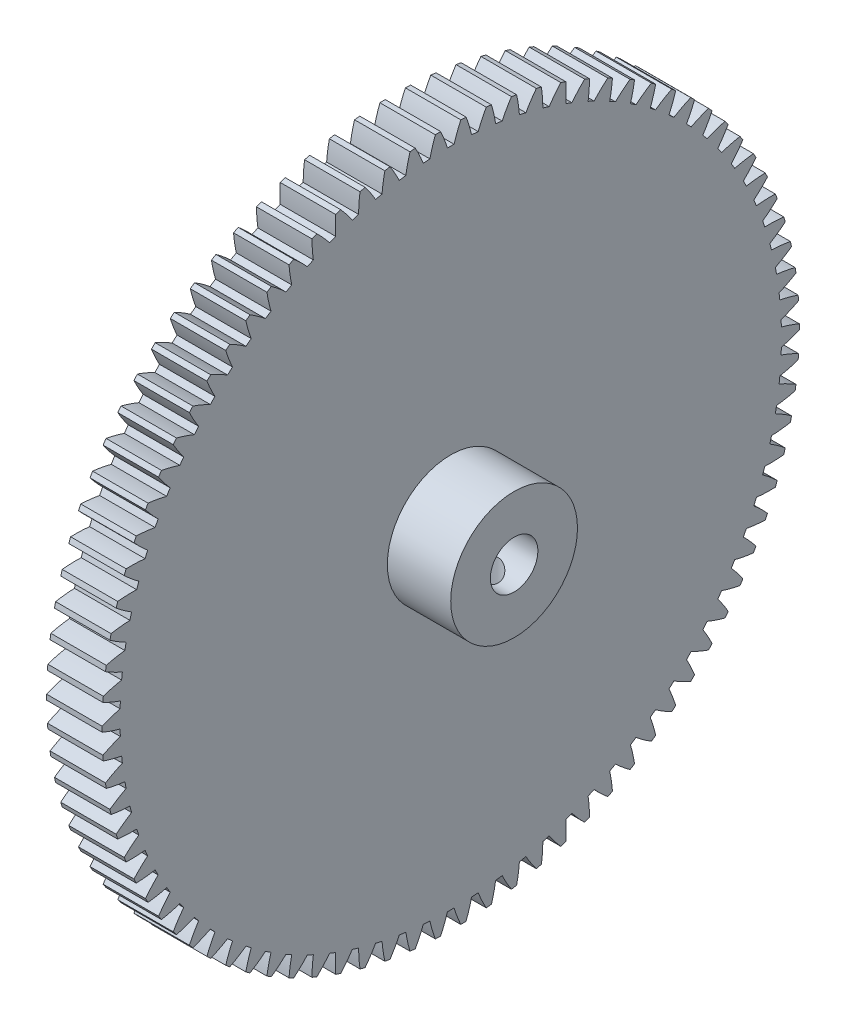
SolidWorks part; units mm, degrees
ref_plane "Plane1" through (0, 0, 0) normal (0, 0, 1) x (1, 0, 0)
ref_plane "Plane2" through (0, 0, 0) normal (0, 1, 0) x (1, 0, 0)
ref_plane "Plane3" through (0, 0, 0) normal (1, 0, 0) x (0, 0, -1)
other "Configuration Table"
sketch "HoldingSke" plane through (0, 0, 0) normal (0, 1, 0) x (1, 0, 0)
  line L0 (0, 0) -> (0.0698, -0.9976)
  line L1 (-15, 0) -> (100, 0) construction
  line L2 (0, 0) -> (-2.1039, 2.3779)
  line L3 (0, 0) -> (-11.863, 4.5341)
  line L4 (0, 0) -> (0.6024, 8.615)
  line L5 (0, 0) -> (-46.8476, -17.4728)
  line L6 (0, 0) -> (-5.8027, -3.9151)
  line L7 (-2.1039, 2.3779) -> (8.6586, 51.2059)
  line L8 (-76.2, 54.61) -> (-75.2, 54.61)
  line L9 (-71.009, 38.7566) -> (-53.1078, 45.2721)
  line L10 (-76.2, 71.12) -> (104.1128, 71.12)
  line L11 (0, 0) -> (-7, 0)
  line L12 (-76.2, 101.6) -> (-76.162, 101.6)
  line L13 (24.9733, 27.94) -> (52.9518, 28.4284)
  line L14 (24.9733, 27.94) -> (24.9743, 27.94)
  line L15 (24.9733, 27.94) -> (100.4006, 29.5858)
  line L16 (-63.627, -1) -> (-12.827, -1)
  circle A0 centre (0, 0) radius 3
  circle A1 centre (0, 0) radius 37.5
  circle A2 centre (0, 0) radius 37.5
  circle A3 centre (0, 0) radius 3
  dimension "MHD" = 75
  dimension "Hub_dia" = 75
  dimension "Bore" = 6
  dimension "MBD" = 6
  dimension "Num_teeth" = 86
  dimension "Pitch" = 1
  dimension "Overall_len" = 50
  dimension "Show_teeth" = 86
  dimension "Thickness" = 7
  dimension "OAL" = 50.0001
  dimension "T_dim" = 1
  dimension "Ap" = 20
  dimension "H" = 19.05
  dimension "Pitch_radius" = 180.3128
  dimension "Width" = 7
  dimension "Backlash" = 0.038
  dimension "Addendum_fac" = 1
  dimension "Dedendum_fac" = 1.25
  dimension "Clearance_fac" = 0.25
  dimension "Dedendum_add" = 0.001
  dimension "Module" = 1
sketch "BasProSke" plane through (0, 0, 0) normal (0, 1, 0) x (1, 0, 0)
  line L0 (-10, 0) -> (60, 0) construction
  line L1 (0, 0) -> (0, 44)
  line L2 (0, 0) -> (7, 0)
  line L3 (7, 0) -> (7, 44)
  line L4 (7, 44) -> (0, 44)
  dimension "Thickness" = 7
  dimension "Diameter" = 88
revolve "Base-Revolve" add sketch "BasProSke" angle 360 about L0
sketch "TooCutSke" plane through (0, 0, 0) normal (1, 0, 0) x (0, 0, -1)
  line L1 (0, 0) -> (0, 107) construction
  line L2 (0, 0) -> (-0.8519, 42.9916) construction
  line L3 (0, 0) -> (-3.1405, 85.9306) construction
  line L4 (-0.8519, 42.9916) -> (-1.5702, 42.9653) construction
  arc A0 (0.4185, 41.7469) -> (-0.4185, 41.7469) centre (0, 0) ccw
  arc A1 (1.2875, 44.0066) -> (-1.2875, 44.0066) centre (0, 0) ccw
  circle A2 centre (0, 0) radius 43 construction
  circle A3 centre (0, 0) radius 40.4068 construction
  arc A4 (-0.4185, 41.7469) -> (-1.2875, 44.0066) centre (-16.8669, 36.718) ccw
  arc A5 (1.2875, 44.0066) -> (0.4185, 41.7469) centre (16.8669, 36.718) ccw
  dimension "Root_dia" = 83.498
  dimension "Overcut_dia" = 88.0508
  dimension "Pitch_dia" = 86
  dimension "Base_dia" = 80.8136
  dimension "Flank_rad" = 17.2
  dimension "Half_ang" = 2.093
  dimension "Half_CT" = 0.7189
extrude "ToothCut" cut sketch "TooCutSke" along normal through all
fillet "Breaks" [suppressed] radius 0.02
fillet "RootFillets" [suppressed] radius 0.251
pattern_circular "TeethCuts" count 86 every 4.186 about axis through (-10, 0, 0) along (1, 0, 0) of "ToothCut", "RootFillets", "Breaks"
sketch "HubNeaOneSke" plane through (0, 0, 0) normal (-1, 0, 0) x (0, 0, 1)
  circle A0 centre (0, 0) radius 37.5
  dimension "Diameter" = 75
extrude "HubNearOne" [suppressed] add sketch "HubNeaOneSke" along normal blind 43.0001
sketch "HubNeaBotSke" plane through (0, 0, 0) normal (-1, 0, 0) x (0, 0, 1)
  circle A0 centre (0, 0) radius 37.5
  dimension "Diameter" = 75
extrude "HubNearBoth" [suppressed] add sketch "HubNeaBotSke" along normal blind 21.5
ref_plane "FarPln" through (7, 0, 0) normal (1, 0, 0) x (0, 0, -1)
sketch "HubFarSke" plane through (7, 0, 0) normal (1, 0, 0) x (0, 0, -1)
  circle A0 centre (0, 0) radius 37.5
  dimension "Diameter" = 75
extrude "HubFar" [suppressed] add sketch "HubFarSke" along normal blind 21.5
sketch "BorSke" plane through (0, 0, 0) normal (1, 0, 0) x (0, 0, -1)
  circle A0 centre (0, 0) radius 3
  dimension "Diameter" = 6
extrude "Bore" cut sketch "BorSke" along normal mid plane 100.0001
sketch "KeySke" plane through (0, 0, 0) normal (1, 0, 0) x (0, 0, -1)
  line L0 (-1, 0) -> (-1, 4)
  line L1 (-1, 4) -> (1, 4)
  line L2 (1, 4) -> (1, 0)
  line L3 (0, 0) -> (0, 34) construction
  line L4 (-1, 0) -> (1, 0)
  dimension "Offset" = 4
  dimension "Width" = 2
extrude "Keyway" [suppressed] cut sketch "KeySke" along normal mid plane 100.0001
pattern_circular "Keyway2" [suppressed] count 2 every 90 about axis through (-10, 0, 0) along (1, 0, 0)
sketch "Croquis1" plane through (7, 0, 0) normal (1, 0, 0) x (0, 0, -1)
  circle A0 centre (0, 0) radius 3
  circle A1 centre (0, 0) radius 8
  dimension "D1" = 6
  dimension "D2" = 16
extrude "Saliente-Extruir1" add sketch "Croquis1" along normal blind 8
sketch "Croquis2" plane through (0, 0, 0) normal (0, 1, 0) x (1, 0, 0)
  line L0 (15, -8) -> (15, 8) construction
  circle A0 centre (11, 0) radius 2
  dimension "D2" = 4
  dimension "D1" = 4
extrude "Cortar-Extruir1" cut sketch "Croquis2" against normal blind 8
equation "' \"Module@HoldingSke\" = 6.35"
equation "' \"Num_teeth@HoldingSke\" = 12"
equation "' \"Ap@HoldingSke\" =  20"
equation "' \"Ap@HoldingSke\" = 20"
equation "' \"Width@HoldingSke\" = 0.5 * 25.4"
equation "' \"Hub_dia@HoldingSke\"= 1 * 25.4"
equation "' \"Hub_dia@HoldingSke\" = 1 * 25.4"
equation "' \"Overall_len@HoldingSke\" = 1.0 * 25.4"
equation "' \"Bore@HoldingSke\" = 0.75 * 25.4"
equation "' \"T_dim@HoldingSke\" = 0.1 * 25.4"
equation "' \"Width@KeySke\" = 0.25 * 25.4"
equation "' \"Show_teeth@HoldingSke\" = 13"
equation "' \"Backlash@HoldingSke\" = 0.009 * 25.4"
equation "' \"Addendum_fac@HoldingSke\" = 1.0"
equation "' \"Dedendum_fac@HoldingSke\" = 1.25"
equation "' \"Dedendum_add@HoldingSke\" = 0.00005 * 25.4"
equation "' \"Clearance_fac@HoldingSke\" = 0.25"
equation "\"Pitch@HoldingSke\" = 1 / \"Module@HoldingSke\""
equation "\"Overcut_dia@TooCutSke\" = (\"Num_teeth@HoldingSke\" + 2 * \"Addendum_fac@HoldingSke\") / \"Pitch@HoldingSke\" + 0.002 * 25.4"
equation "\"Pitch_dia@TooCutSke\" = \"Num_teeth@HoldingSke\" / \"Pitch@HoldingSke\""
equation "\"Base_dia@TooCutSke\" = \"Num_teeth@HoldingSke\" / \"Pitch@HoldingSke\" * cos((\"Ap@HoldingSke\"  * 3.14159265 / 180))"
equation "\"Root_dia@TooCutSke\" = (\"Num_teeth@HoldingSke\" + 2) / \"Pitch@HoldingSke\" - 2 * (\"Addendum_fac@HoldingSke\" + \"Dedendum_fac@HoldingSke\") / \"Pitch@HoldingSke\" - \"Dedendum_add@HoldingSke\" * 2"
equation "\"Half_ang@TooCutSke\" = 180 / \"Num_teeth@HoldingSke\""
equation "\"Half_CT@TooCutSke\" = \"Num_teeth@HoldingSke\" / \"Pitch@HoldingSke\" * sin((3.14159265 / 2 / \"Num_teeth@HoldingSke\")) / 2 - 7 * \"Backlash@HoldingSke\" / 4"
equation "\"Flank_rad@TooCutSke\" = \"Num_teeth@HoldingSke\" / \"Pitch@HoldingSke\" / 5"
equation "\"Radius@RootFillets\" = \"Clearance_fac@HoldingSke\" / \"Pitch@HoldingSke\" + \"Dedendum_add@HoldingSke\""
equation "\"Break_rad@Breaks\" = 0.02 / \"Pitch@HoldingSke\""
equation "\"Thickness@HoldingSke\" = \"Width@HoldingSke\""
equation "\"OAL@HoldingSke\" = \"Thickness@HoldingSke\""
equation "\"MHD@HoldingSke\" = (\"Num_teeth@HoldingSke\" + 2) / \"Pitch@HoldingSke\" - 2 * (\"Addendum_fac@HoldingSke\" + \"Dedendum_fac@HoldingSke\")  / \"Pitch@HoldingSke\" - \"Dedendum_add@HoldingSke\" * 2"
equation "\"MBD@HoldingSke\" = (\"Num_teeth@HoldingSke\" + 2) / \"Pitch@HoldingSke\" - 2 * (\"Addendum_fac@HoldingSke\" + \"Dedendum_fac@HoldingSke\")  / \"Pitch@HoldingSke\" - \"Dedendum_add@HoldingSke\" * 2 - 0.002 * 25.4"
equation "\"MHD@HoldingSke\" = ((sgn( \"MHD@HoldingSke\" - \"Hub_dia@HoldingSke\" )-1)*( \"MHD@HoldingSke\" - \"Hub_dia@HoldingSke\" ))/-2+ \"Hub_dia@HoldingSke\""
equation "\"MBD@HoldingSke\" = ((sgn( \"MBD@HoldingSke\" - \"Bore@HoldingSke\" )-1)*( \"MBD@HoldingSke\" - \"Bore@HoldingSke\" ))/-2+ \"Bore@HoldingSke\""
equation "\"OAL@HoldingSke\" = ((sgn( \"OAL@HoldingSke\" - \"Overall_len@HoldingSke\" )+1)*( \"OAL@HoldingSke\" - \"Overall_len@HoldingSke\" ))/2 + \"Overall_len@HoldingSke\" + 0.000002 * 25.4"
equation "\"Num_teeth@TeethCuts\" = int( \"Show_teeth@HoldingSke\" ) + 1"
equation "\"Num_teeth@TeethCuts\" = ((sgn( \"Num_teeth@TeethCuts\" - \"Num_teeth@HoldingSke\" )-1)*( \"Num_teeth@TeethCuts\" - \"Num_teeth@HoldingSke\" ))/-2+ \"Num_teeth@HoldingSke\""
equation "\"Num_teeth@TeethCuts\" = ((sgn( \"Num_teeth@TeethCuts\" - 2.0)+1)*( \"Num_teeth@TeethCuts\" - 2.0))/2 +2.0"
equation "\"Angle@TeethCuts\" = 360.0 / \"Num_teeth@HoldingSke\""
equation "\"Diameter@BasProSke\" = (\"Num_teeth@HoldingSke\" + 2 * \"Addendum_fac@HoldingSke\") / \"Pitch@HoldingSke\""
equation "\"Thickness@BasProSke\"  = \"Thickness@HoldingSke\""
equation "' \"Fillet_rad@BasProSke\" =  \"Thickness@HoldingSke\" * 0.05"
equation "' \"Fillet_rad@BasProSke\" = \"Thickness@HoldingSke\" * 0.05"
equation "\"MHD@HoldingSke\" = ((sgn( \"MHD@HoldingSke\" - \"Root_dia@TooCutSke\" )-1)*( \"MHD@HoldingSke\" - \"Root_dia@TooCutSke\" ))/-2+ \"Root_dia@TooCutSke\""
equation "\"Diameter@HubNeaOneSke\" = \"MHD@HoldingSke\""
equation "\"Length@HubNearOne\" = \"OAL@HoldingSke\" - \"Thickness@BasProSke\""
equation "\"Diameter@HubNeaBotSke\" = \"MHD@HoldingSke\""
equation "\"Length@HubNearBoth\" = ( \"OAL@HoldingSke\" - \"Thickness@BasProSke\" ) / 2.0"
equation "\"Thickness@FarPln\" = \"Thickness@BasProSke\""
equation "\"Diameter@HubFarSke\" = \"MHD@HoldingSke\""
equation "\"Length@HubFar\" = ( \"OAL@HoldingSke\" - \"Thickness@BasProSke\" ) / 2.0"
equation "\"Diameter@BorSke\" = \"MBD@HoldingSke\""
equation "\"D1@Bore\" = \"OAL@HoldingSke\" * 2.0"
equation "\"D1@Keyway\" = \"OAL@HoldingSke\" * 2.0"
equation "\"Offset@KeySke\" = \"T_dim@HoldingSke\" + \"MBD@HoldingSke\" / 2.0"
